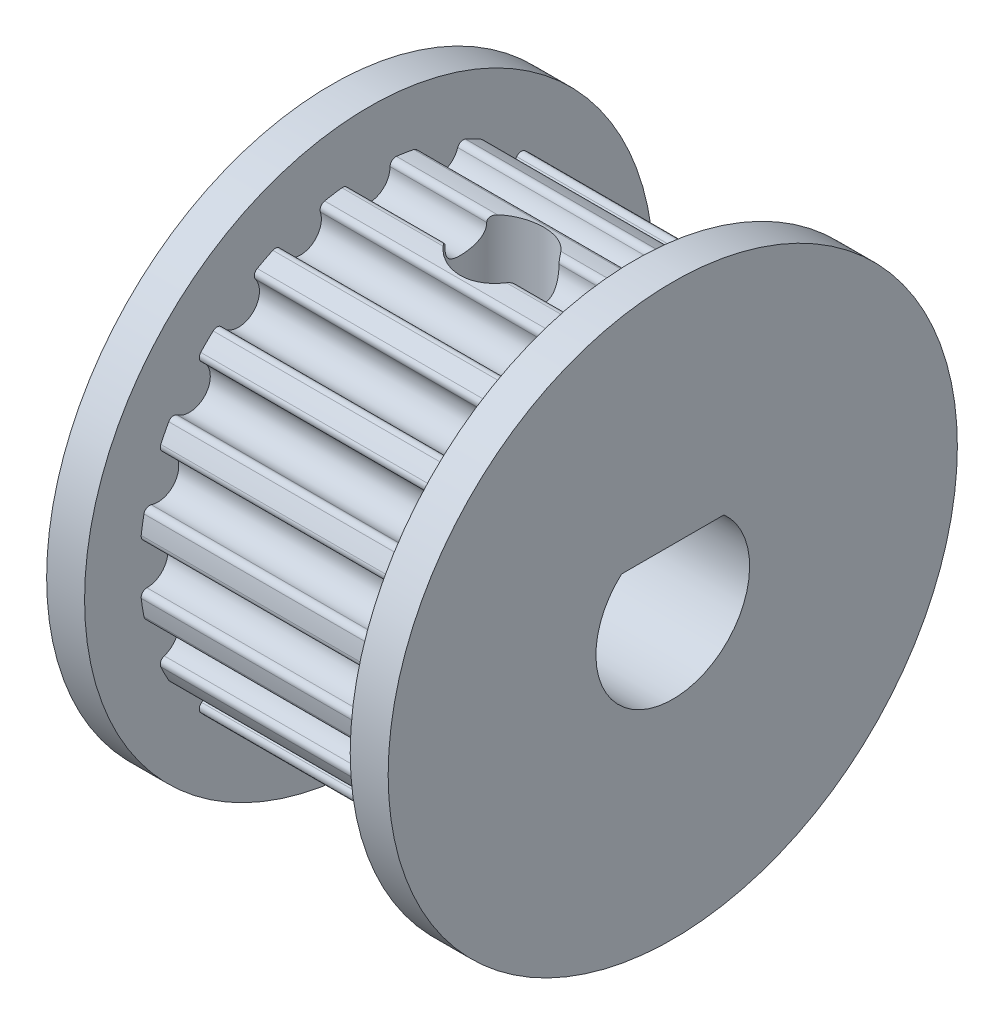
SolidWorks part; units mm, degrees
material "Alloy Steel"
ref_plane "Сверху" through (0, 0, 0) normal (0, 0, 1) x (1, 0, 0)
ref_plane "Справа" through (0, 0, 0) normal (0, 1, 0) x (1, 0, 0)
ref_plane "Спереди" through (0, 0, 0) normal (1, 0, 0) x (0, 0, -1)
sketch "Эскиз1" plane through (0, 0, 0) normal (0, 0, 1) x (1, 0, 0)
  line L0 (0, 7.5) -> (0, 0)
  line L3 (0, 7.5) -> (1, 7.5)
  line L4 (1, 6.05) -> (8, 6.05)
  line L5 (8, 6.05) -> (8, 7.5)
  line L7 (9, 0) -> (9, 7.5)
  line L11 (0, 0) -> (9, 0)
  line L12 (1, 7.5) -> (1, 6.05)
  line L13 (8, 7.5) -> (9, 7.5)
  dimension "D1" = 7.5
  dimension "D2" = 1
  dimension "D6" = 6.05
  dimension "D8" = 7
revolve "Body" add sketch "Эскиз1" angle 360 about L11
sketch "Эскиз3" plane through (1, 0, 0) normal (1, 0, 0) x (0, 0, -1)
  line L0 (0, 0) -> (9.7637, 0) construction
  circle A0 centre (5.5684, -1.8093) radius 0.55
  circle A2 centre (4.7368, -3.4415) radius 0.55
  circle A3 centre (3.4415, -4.7368) radius 0.55
  circle A4 centre (1.8093, -5.5684) radius 0.55
  circle A5 centre (0, -5.855) radius 0.55
  circle A6 centre (5.855, 0) radius 0.55
  circle A7 centre (-1.8093, -5.5684) radius 0.55
  circle A8 centre (-3.4415, -4.7368) radius 0.55
  circle A9 centre (-4.7368, -3.4415) radius 0.55
  circle A10 centre (-5.5684, -1.8093) radius 0.55
  circle A11 centre (-5.855, 0) radius 0.55
  circle A12 centre (-5.5684, 1.8093) radius 0.55
  circle A13 centre (-4.7368, 3.4415) radius 0.55
  circle A14 centre (-3.4415, 4.7368) radius 0.55
  circle A17 centre (-1.8093, 5.5684) radius 0.55
  circle A18 centre (0, 5.855) radius 0.55
  circle A19 centre (1.8093, 5.5684) radius 0.55
  circle A20 centre (3.4415, 4.7368) radius 0.55
  circle A21 centre (4.7368, 3.4415) radius 0.55
  circle A22 centre (5.5684, 1.8093) radius 0.55
  point P45 (0, 0)
  dimension "D1" = 5.855
  dimension "D2" = 20
  dimension "D3" = 1.1
extrude "20tooth" cut sketch "Эскиз3" along normal blind 7
fillet "Скругление1" radius 0.15 40 edges at (4.5, 0.5223, -6.0274) (4.5, -0.5223, -6.0274) (4.5, -1.3659, -5.8938) (4.5, -2.3593, -5.571) (4.5, -3.1203, -5.1833) (4.5, -3.9654, -4.5693) (4.5, -4.5693, -3.9654) (4.5, -5.1833, -3.1203) (4.5, -5.571, -2.3593) (4.5, -5.8938, -1.3659) (4.5, -6.0274, -0.5223) (4.5, -6.0274, 0.5223) (4.5, -5.8938, 1.3659) (4.5, -5.571, 2.3593) (4.5, -5.1833, 3.1203) (4.5, -4.5693, 3.9654) (4.5, -3.9654, 4.5693) (4.5, -3.1203, 5.1833) (4.5, -2.3593, 5.571) (4.5, -1.3659, 5.8938) (4.5, -0.5223, 6.0274) (4.5, 0.5223, 6.0274) (4.5, 1.3659, 5.8938) (4.5, 2.3593, 5.571) (4.5, 3.1203, 5.1833) (4.5, 3.9654, 4.5693) (4.5, 4.5693, 3.9654) (4.5, 5.1833, 3.1203) (4.5, 5.571, 2.3593) (4.5, 5.8938, 1.3659) (4.5, 6.0274, 0.5223) (4.5, 6.0274, -0.5223) (4.5, 5.8938, -1.3659) (4.5, 5.571, -2.3593) (4.5, 5.1833, -3.1203) (4.5, 4.5693, -3.9654) (4.5, 3.9654, -4.5693) (4.5, 3.1203, -5.1833) (4.5, 2.3593, -5.571) (4.5, 1.3659, -5.8938)
sketch "Sketch1" plane through (9, 0, 0) normal (1, 0, 0) x (0, 0, -1)
  line L0 (-1.35, 1.5093) -> (1.35, 1.5093)
  arc A0 (-1.35, 1.5093) -> (1.35, 1.5093) centre (0, 0) ccw
  dimension "D1" = 4.05
  dimension "D2" = 2.7
extrude "Cut-Extrude1" cut sketch "Sketch1" against normal through all
hole_wizard "M2 Clearance Hole1" positions "Sketch3" profile "Sketch2" hole size "M2" standard "DIN"
sketch "Sketch3" plane through (0, 1.5093, 0) normal (0, -1, 0) x (-1, 0, 0)
  line L0 (0, 0) -> (-9, 0) construction
  line L3 (0, 1.35) -> (0, -1.35) construction
  line L4 (-9, 1.35) -> (-9, -1.35) construction
  point P0 (-4.5, 0)
sketch "Sketch2" plane through (4.5, 1.5093, 0) normal (1, 0, 0) x (0, 0, -1)
  line L0 (0, 0) -> (0, 5.9907)
  line L1 (0, 5.9907) -> (1.1, 5.9907)
  line L2 (1.1, 5.9907) -> (1.1, 0)
  line L5 (1.1, 0) -> (0, 0)
  line L11 (0, -6.35) -> (0, 107.95) construction
  dimension "Thru Hole Dia." = 2.2
  dimension "Thru Hole Depth" = 5.9907
